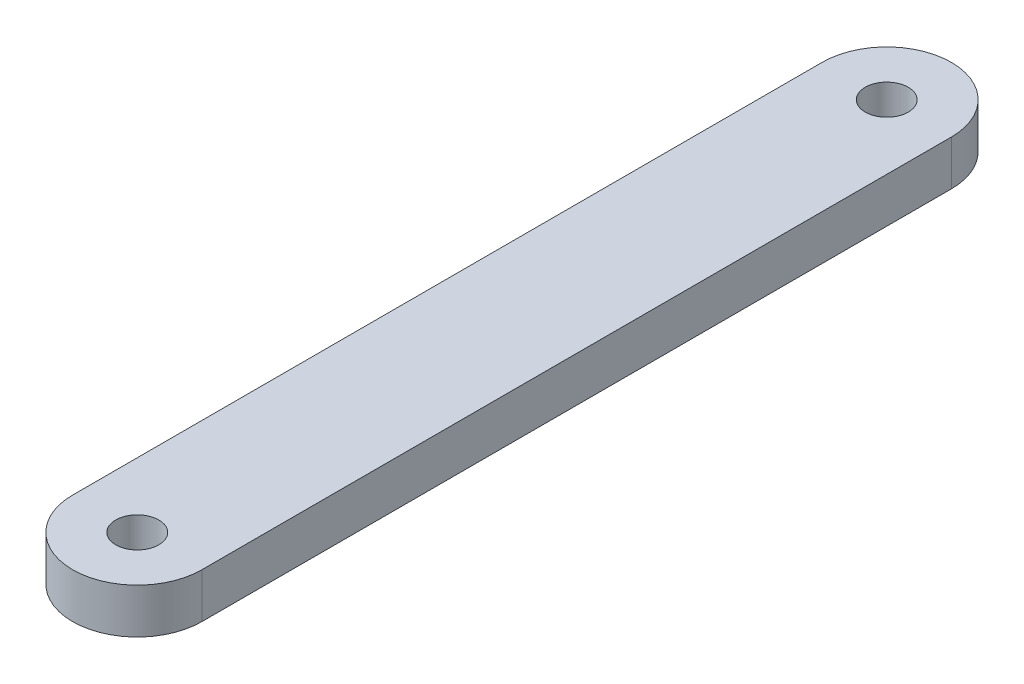
SolidWorks part; units mm, degrees
material "Acrylic (Medium-high impact)"
ref_plane "Front Plane" through (0, 0, 0) normal (0, 0, 1) x (1, 0, 0)
ref_plane "Top Plane" through (0, 0, 0) normal (0, 1, 0) x (1, 0, 0)
ref_plane "Right Plane" through (0, 0, 0) normal (1, 0, 0) x (0, 0, -1)
sketch "Sketch1" plane through (0, 0, 0) normal (0, 1, 0) x (1, 0, 0)
  line L0 (-4.3815, 50.8) -> (-4.3815, 0)
  line L1 (4.3815, 50.8) -> (4.3815, 0)
  circle A0 centre (0, 0) radius 1.4605
  arc A1 (-4.3815, 0) -> (4.3815, 0) centre (0, 0) ccw
  circle A2 centre (0, 50.8) radius 1.4605
  arc A3 (4.3815, 50.8) -> (-4.3815, 50.8) centre (0, 50.8) ccw
  dimension "D1" = 2.921
  dimension "D2" = 2.921
  dimension "D4" = 2.921
  dimension "D3" = 50.8
extrude "Boss-Extrude1" add sketch "Sketch1" along normal blind 3.048
